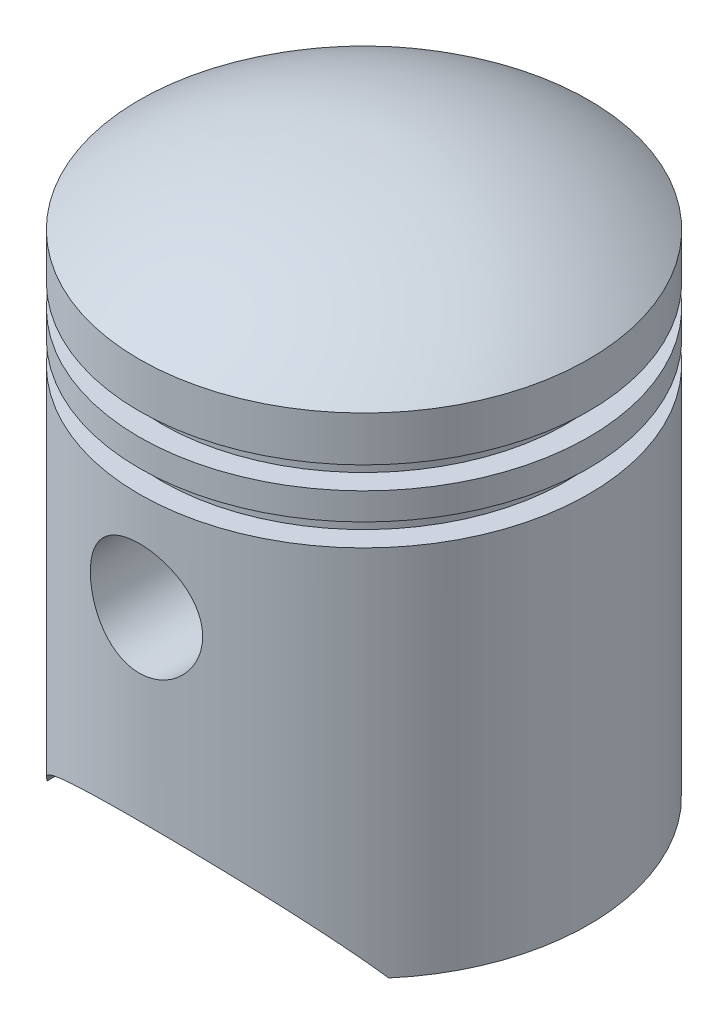
SolidWorks part; units mm, degrees
ref_plane "Front Plane" through (0, 0, 0) normal (0, 0, 1) x (1, 0, 0)
ref_plane "Top Plane" through (0, 0, 0) normal (0, 1, 0) x (1, 0, 0)
ref_plane "Right Plane" through (0, 0, 0) normal (1, 0, 0) x (0, 0, -1)
sketch "Sketch1" plane through (0, 0, 0) normal (0, 0, 1) x (1, 0, 0)
  line L0 (0, 62.5) -> (0, 60.4994)
  line L1 (23, 0) -> (25, 0)
  line L2 (25, 0) -> (25, 41.5)
  line L3 (25, 41.5) -> (22.5, 41.5)
  line L4 (22.5, 41.5) -> (22.5, 44)
  line L5 (22.5, 44) -> (25, 44)
  line L6 (25, 44) -> (25, 47)
  line L7 (25, 47) -> (22.5, 47)
  line L8 (22.5, 47) -> (22.5, 49.5)
  line L9 (22.5, 49.5) -> (25, 49.5)
  line L10 (25, 49.5) -> (25, 54.5)
  line L12 (0, 62.5) -> (0, 0) construction
  line L13 (23, 0) -> (23, 39.5)
  line L14 (23, 39.5) -> (20.5, 39.5)
  line L15 (20.5, 39.5) -> (20.5, 45.5)
  line L16 (20.5, 45.5) -> (20.5, 45.5)
  line L17 (20.5, 45.5) -> (20.5, 45.5)
  line L18 (20.5, 45.5) -> (20.5, 45.5)
  line L19 (20.5, 45.5) -> (20.5, 51.5)
  line L20 (20.5, 51.5) -> (23, 51.5)
  line L21 (23, 51.5) -> (23, 53.4845)
  line L22 (23, 2) -> (23, 39.5) construction
  line L23 (2, 2) -> (23, 2) construction
  line L24 (0, 0) -> (25, 0) construction
  line L25 (2, 60.4985) -> (2, 2) construction
  arc A0 (25, 54.5) -> (0, 62.5) centre (0.9839, 22.5121) ccw
  arc A1 (23, 53.4845) -> (0, 60.4994) centre (0.9839, 22.5121) ccw
  arc A2 (23, 53.4845) -> (2, 60.4985) centre (0.9839, 22.5121) ccw construction
  dimension "D8" = 40
  dimension "D3" = 41.5
  dimension "D4" = 2.5
  dimension "D5" = 2.5
  dimension "D6" = 3
  dimension "D7" = 5
  dimension "D9" = 2
revolve "Revolve1" add sketch "Sketch1" angle 360 about L0
sketch "Sketch2" plane through (0, 0, 0) normal (0, 0, 1) x (1, 0, 0)
  line L0 (19, 0) -> (-19, 0)
  line L1 (-25, 0) -> (25, 0) construction
  line L2 (0, 0) -> (0, 10) construction
  arc A0 (-19, 0) -> (19, 0) centre (0, -13.0454) cw
  dimension "D1" = 10
  dimension "D2" = 38
extrude "Cut-Extrude1" cut sketch "Sketch2" against normal through all both and the other way through all
sketch "Sketch3" plane through (0, 0, 0) normal (0, 0, 1) x (1, 0, 0)
  line L0 (0, 30.5) -> (0, 62.5) construction
  circle A0 centre (0, 30.5) radius 6.25
  point P2 (0, 0)
  dimension "D2" = 12.5
  dimension "D1" = 32
extrude "Cut-Extrude2" cut sketch "Sketch3" against normal through all both and the other way through all
ref_plane "Plane1" through (0, 0, 12) normal (0, 0, 1) x (1, 0, 0)
sketch "Sketch5" plane through (0, 0, 12) normal (0, 0, 1) x (1, 0, 0)
  circle A0 centre (0, 30.5) radius 6.25 construction
  circle A1 centre (0, 30.5) radius 6.25
  circle A2 centre (0, 30.5) radius 7.25
  dimension "D1" = 14.5
extrude "Boss-Extrude1" add sketch "Sketch5" along normal up to next
mirror "Mirror1" about plane through (0, 0, 0) normal (0, 0, 1) of "Boss-Extrude1"
